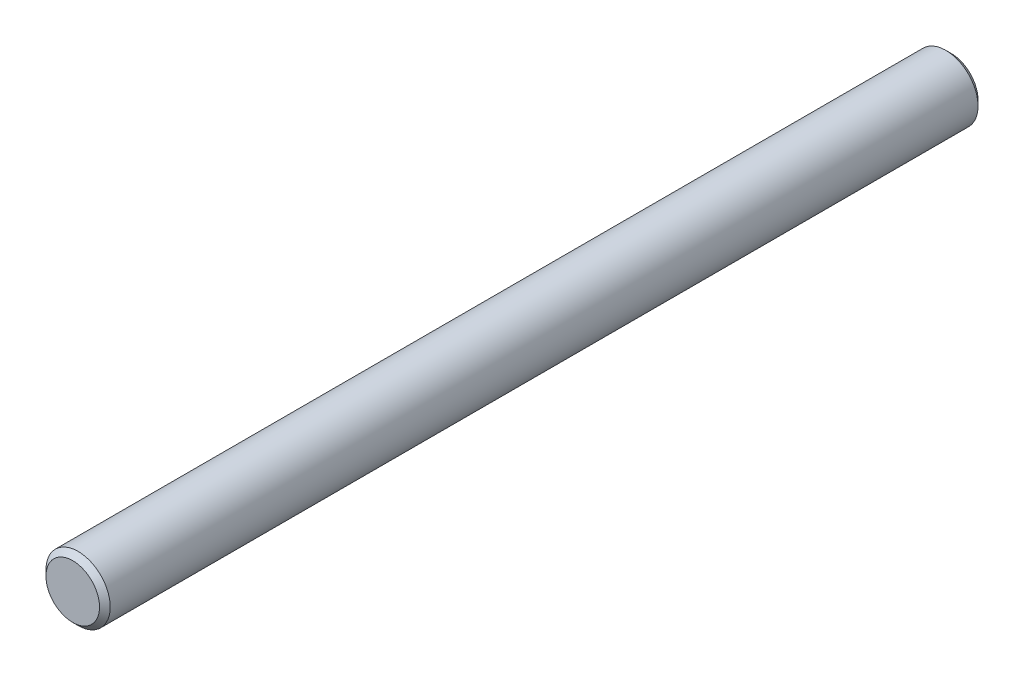
SolidWorks part; units mm, degrees
material "AISI 316 Annealed Stainless Steel Bar (SS)"
ref_plane "Front Plane" through (0, 0, 0) normal (0, 0, 1) x (1, 0, 0)
ref_plane "Top Plane" through (0, 0, 0) normal (0, 1, 0) x (1, 0, 0)
ref_plane "Right Plane" through (0, 0, 0) normal (1, 0, 0) x (0, 0, -1)
sketch "Sketch1" plane through (0, 0, 0) normal (0, 0, 1) x (1, 0, 0)
  circle A0 centre (0, 0) radius 3
  dimension "D1" = 6
extrude "Shaft" add sketch "Sketch1" along normal mid plane 82
cosmetic thread "Cosmetic Thread1" parameters "D1"=10, "D2"=4.891
cosmetic thread "Cosmetic Thread2" parameters "D1"=10, "D2"=4.891
cosmetic thread "Cosmetic Thread3" parameters "D1"=10, "D2"=4.891
chamfer "0.5x45 Chamfers" distance 0.5 angle 45 2 edges at (3, 0, 41) (3, 0, -41)
